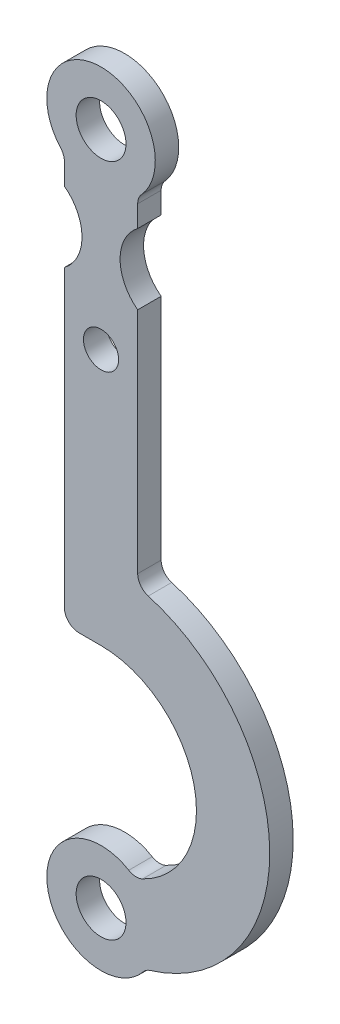
SolidWorks part; units mm, degrees
material "1.0577 (S355J2G4)"
ref_plane "Front Plane" through (0, 0, 0) normal (0, 0, 1) x (1, 0, 0)
ref_plane "Top Plane" through (0, 0, 0) normal (0, 1, 0) x (1, 0, 0)
ref_plane "Right Plane" through (0, 0, 0) normal (1, 0, 0) x (0, 0, -1)
sketch "Sketch1" plane through (0, 0, 0) normal (0, 0, 1) x (1, 0, 0)
  line L0 (-12.5, -13.6382) -> (-12.5, -23)
  line L1 (12.5, -13.6382) -> (12.5, -23)
  line L2 (0, 0) -> (0, -87.0636) construction
  line L3 (-12.5, -47) -> (-12.5, -154.9531)
  line L4 (12.5, -47) -> (12.5, -128.8307)
  line L5 (0, -152.4567) -> (-12.5, -152.4567)
  line L6 (15.2393, -240.4887) -> (11.4444, -215.4646) construction
  line L7 (0, -230) -> (17.3612, -226.5161)
  line L8 (-12.5, -13) -> (12.5, -13) construction
  line L9 (12.5, -57) -> (-12.5, -57) construction
  circle A0 centre (0, 0) radius 8.5
  arc A1 (-12.5, -13.6382) -> (12.5, -13.6382) centre (0, 0) cw
  arc A2 (-12.5, -23) -> (-12.5, -47) centre (-21.5, -35) cw
  arc A3 (12.5, -23) -> (12.5, -47) centre (21.5, -35) ccw
  arc A4 (-12.5, -154.9531) -> (11.4444, -215.4646) centre (0, -185) cw
  arc A5 (11.4444, -215.4646) -> (15.2393, -240.4887) centre (0, -230) ccw
  arc A6 (15.2393, -240.4887) -> (12.5, -128.8307) centre (0, -185) ccw
  circle A7 centre (0, -230) radius 8.5
  arc A8 (0, -230) -> (0, -140) centre (0, -185) ccw construction
  circle A9 centre (0, -65) radius 6
  point P11 (-6.5, -35)
  point P21 (13.3418, -227.9767)
  point P25 (6.5, -35)
  dimension "D1" = 17
  dimension "D2" = 10
  dimension "D3" = 17
  dimension "D4" = 25
  dimension "D7" = 230
  dimension "D9" = 10
  dimension "D11" = 15
  dimension "D12" = 185
  dimension "D13" = 12
  dimension "D10" = 65
  dimension "D5" = 13
  dimension "D6" = 25
  dimension "D8" = 35
  dimension "D14" = 9
  dimension "D15" = 24
  dimension "D16" = 10
  dimension "D17" = 10
extrude "Boss-Extrude1" add sketch "Sketch1" along normal blind 8 contours A5 A6 L4 A3 L1 A1 L0 A2 L3 L5 A4 A7 A0
sketch "Sketch2" plane through (0, 0, 8) normal (0, 0, 1) x (1, 0, 0)
  line L0 (-12.5, -95) -> (-11, -92.4)
  line L1 (-12.5, -47) -> (-12.5, -152.4567) construction
  line L2 (-11, -92.4) -> (-11, -99.5)
  line L3 (-11, -99.5) -> (-10.5, -100)
  line L4 (-10.5, -100) -> (-4.1667, -100)
  line L7 (-10.5, -100) -> (-11, -100.5)
  line L8 (-11, -100.5) -> (-11, -107.6)
  line L9 (-11, -107.6) -> (-12.5, -105)
  line M16 (-12.5, -47) -> (-12.5, -152.4567)
  dimension "D1" = 10
  dimension "D2" = 1.5
  dimension "D3" = 2
  dimension "D4" = 1
  dimension "D5" = 7.6
  dimension "D6" = 8.3333
  dimension "D7" = 100
extrude "Cut-Extrude1" [suppressed] cut sketch "Sketch2" against normal through all contours L9 L8 L7 L3 L2 L0 M16
fillet "Fillet1" radius 5 6 edges at (15.2393, -240.4887, 4) (11.4444, -215.4646, 4) (12.5, -13.6382, 4) (-12.5, -13.6382, 4) (12.5, -128.8307, 4) (-12.5, -152.4567, 4)
